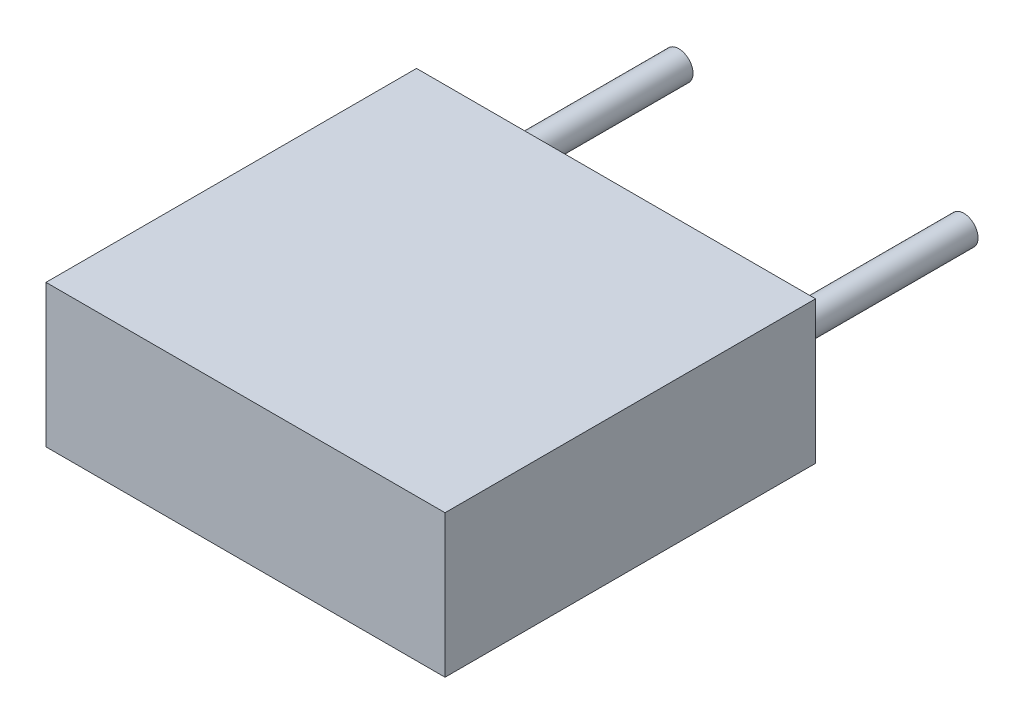
SolidWorks part; units mm, degrees
ref_plane "Plan de face" through (0, 0, 0) normal (0, 0, 1) x (1, 0, 0)
ref_plane "Plan de dessus" through (0, 0, 0) normal (0, 1, 0) x (1, 0, 0)
ref_plane "Plan de droite" through (0, 0, 0) normal (1, 0, 0) x (0, 0, -1)
sketch "Esquisse1" plane through (0, 0, 0) normal (0, 0, 1) x (1, 0, 0)
  line L1 (-3.5, -1.25) -> (3.5, -1.25)
  line L2 (-3.5, -1.25) -> (-3.5, 1.25)
  line L3 (-3.5, 1.25) -> (3.5, 1.25)
  line L4 (3.5, -1.25) -> (3.5, 1.25)
  line L5 (-3.5, -1.25) -> (3.5, 1.25) construction
  line L6 (-3.5, 1.25) -> (3.5, -1.25) construction
  point P0 (0, 0)
  dimension "D1" = 2.5
  dimension "D2" = 7
extrude "Boss.-Extru.1" add sketch "Esquisse1" along normal blind 6.5
sketch "Esquisse2" plane through (0, 0, 0) normal (0, 0, -1) x (-1, 0, 0)
  line L0 (-2.5, 0) -> (0, 0) construction
  line L1 (0, 0) -> (2.5, 0) construction
  circle A0 centre (-2.5, 0) radius 0.25
  circle A1 centre (2.5, 0) radius 0.25
  dimension "D1" = 0.5
  dimension "D2" = 5
extrude "Boss.-Extru.2" add sketch "Esquisse2" along normal blind 3.6
